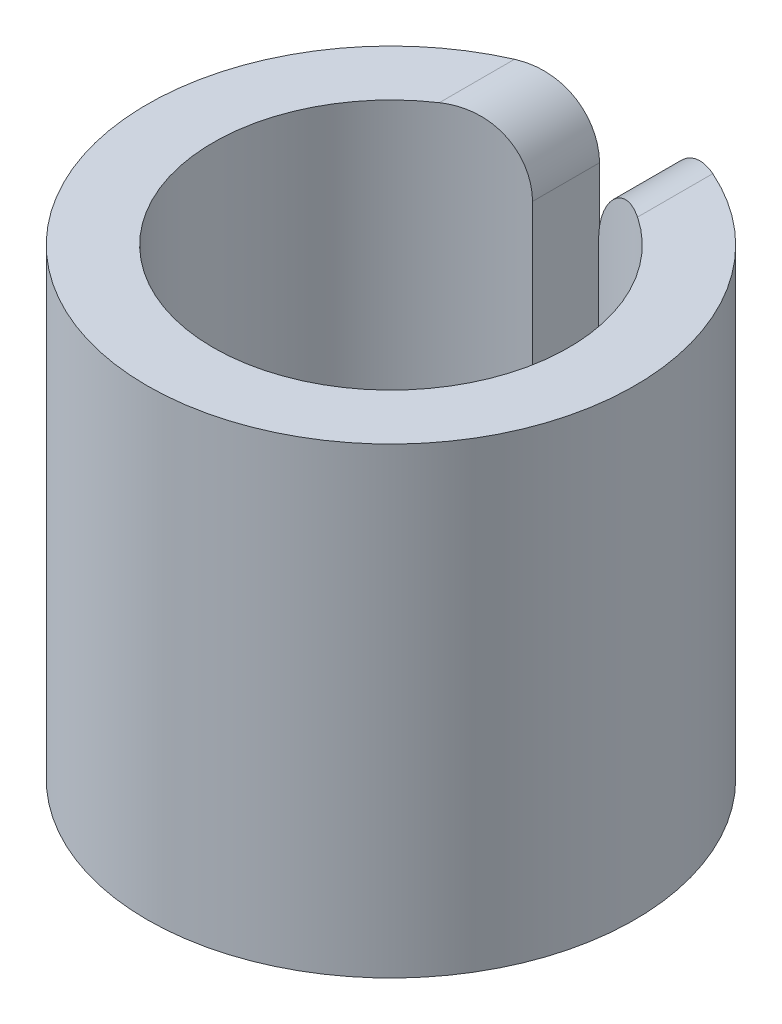
SolidWorks part; units mm, degrees
ref_plane "Front Plane" through (0, 0, 0) normal (0, 0, 1) x (1, 0, 0)
ref_plane "Top Plane" through (0, 0, 0) normal (0, 1, 0) x (1, 0, 0)
ref_plane "Right Plane" through (0, 0, 0) normal (1, 0, 0) x (0, 0, -1)
sketch "Sketch3" plane through (0, 0, 0) normal (0, 1, 0) x (1, 0, 0)
  circle A0 centre (0, 0) radius 2.69
  point P4 (0, 0)
  point P5 (0.3031, 9.02)
  dimension "D1" = 5.38
extrude "Extrude-Thin1" add sketch "Sketch3" along normal mid plane 7 thin
sketch "Sketch4" plane through (0, 0, 0) normal (0, 1, 0) x (1, 0, 0)
  line L5 (0.5, 0) -> (-0.5, 0)
  line L6 (0.5, 0) -> (0.5, 1000)
  line L7 (0.5, 1000) -> (-0.5, 1000)
  line L8 (-0.5, 0) -> (-0.5, 1000)
  circle A1 centre (0, 0) radius 3.69 construction
  point P4 (0, 0)
  dimension "D1" = 1
  dimension "D2" = 1000
extrude "Cut-Extrude1" cut sketch "Sketch4" against normal through all both and the other way through all
fillet "Fillet1" radius 1 4 edges at (0.5, 3.5, -3.1495) (-0.5, 3.5, -3.1495) (-0.5, -3.5, -3.1495) (0.5, -3.5, -3.1495)
